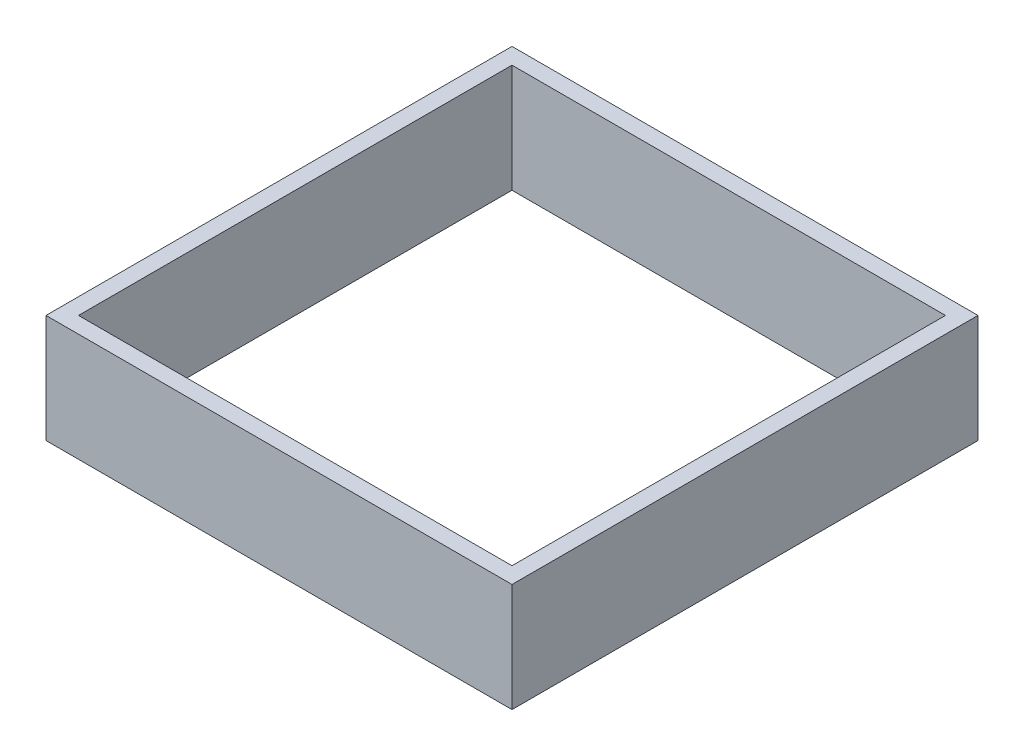
SolidWorks part; units mm, degrees
ref_plane "Front Plane" through (0, 0, 0) normal (0, 0, 1) x (1, 0, 0)
ref_plane "Top Plane" through (0, 0, 0) normal (0, 1, 0) x (1, 0, 0)
ref_plane "Right Plane" through (0, 0, 0) normal (1, 0, 0) x (0, 0, -1)
sketch "Sketch1" plane through (0, 0, 0) normal (0, 1, 0) x (1, 0, 0)
  line L0 (21.5, 21.5) -> (-21.5, 21.5)
  line L1 (20, -20) -> (-20, -20)
  line L2 (20, -20) -> (20, 20)
  line L3 (20, 20) -> (-20, 20)
  line L4 (-20, -20) -> (-20, 20)
  line L5 (20, -20) -> (-20, 20) construction
  line L6 (20, 20) -> (-20, -20) construction
  line L7 (-21.5, -21.5) -> (-21.5, 21.5)
  line L8 (21.5, -21.5) -> (-21.5, -21.5)
  line L9 (21.5, -21.5) -> (21.5, 21.5)
  point P0 (0, 0)
  dimension "D1" = 40
  dimension "D2" = 1.5
extrude "Boss-Extrude1" add sketch "Sketch1" along normal blind 10
